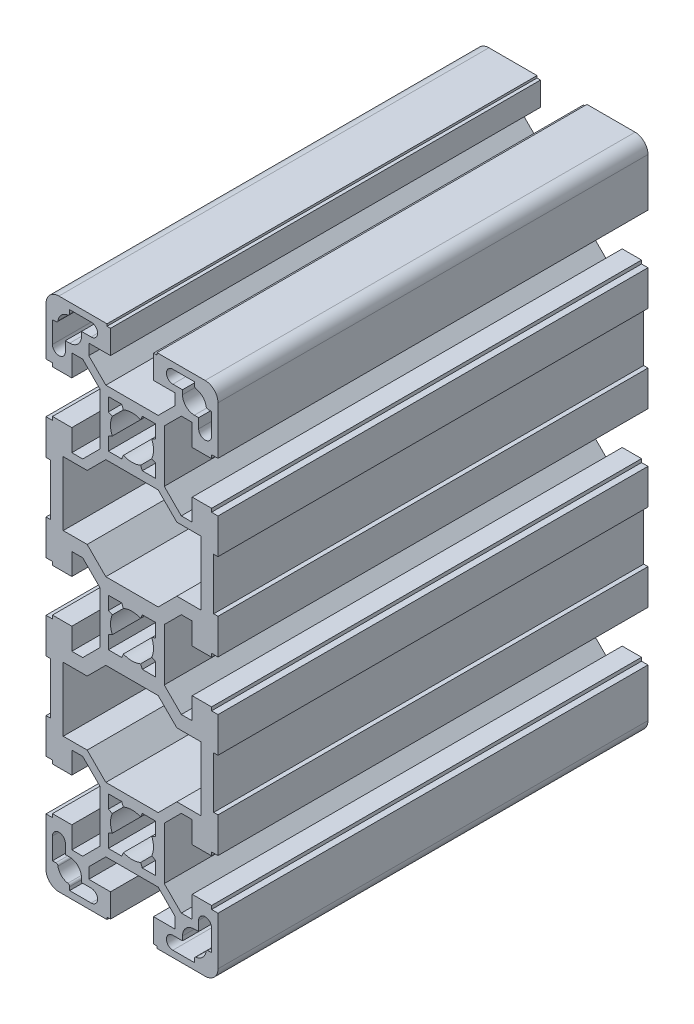
SolidWorks part; units mm, degrees
ref_plane "Front Plane" through (0, 0, 0) normal (0, 0, 1) x (1, 0, 0)
ref_plane "Top Plane" through (0, 0, 0) normal (0, 1, 0) x (1, 0, 0)
ref_plane "Right Plane" through (0, 0, 0) normal (1, 0, 0) x (0, 0, -1)
sketch "Sketch1" plane through (0, 0, 0) normal (0, 0, 1) x (1, 0, 0)
  line L0 (0, 69.0644) -> (0, -69.0644) construction
  line L1 (-42.1374, 0) -> (42.1374, 0) construction
  line L2 (20, -57) -> (20, -45.8)
  line L3 (11.75, -55.5) -> (11.75, -54.5)
  line L4 (5, -54) -> (5, -59.5)
  line L5 (-5, -59.5) -> (-5, -54)
  line L6 (-11.75, -54.5) -> (-11.75, -55.5)
  line L7 (-20, -45.8) -> (-20, -57)
  line L8 (5.8051, -60) -> (17, -60)
  line L9 (14.5, -58.5) -> (9.5, -58.5)
  line L10 (-17, -60) -> (-5.8051, -60)
  line L11 (-11.75, -55.5) -> (-9.5, -55.5)
  line L12 (-9.5, -58.5) -> (-14.5, -58.5)
  line L13 (-14.5, -58.5) -> (-14.5, -57.7113)
  line L14 (-5.8051, -60) -> (-5.8051, -59.5)
  line L15 (-5.8051, -59.5) -> (-5, -59.5)
  line L16 (9.5, -55.5) -> (11.75, -55.5)
  line L17 (5, -59.5) -> (5.8051, -59.5)
  line L18 (5.8051, -59.5) -> (5.8051, -60)
  line L19 (14.5, -57.7113) -> (14.5, -58.5)
  line L21 (18.5, 5) -> (14, 5)
  line L22 (11.4642, -29.95) -> (14, -29.95)
  line L23 (14, -10.05) -> (11.4642, -10.05)
  line L24 (14, -50.05) -> (11.4642, -50.05)
  line L25 (18.5, 5.8) -> (18.5, 5)
  line L26 (20, 5.8) -> (18.5, 5.8)
  line L27 (15.9974, -28.1597) -> (10.4261, -28.1597)
  line L28 (10.4261, -13.2597) -> (15.9974, -13.2597)
  line L29 (11.4642, -10.05) -> (7.5, -6.0858)
  line L30 (6.0884, -8.9219) -> (10.4261, -13.2597)
  line L31 (-7.5, -6.0858) -> (-11.4642, -10.05)
  line L32 (-20, -5.8) -> (-20, -14)
  line L33 (-14, -10.05) -> (-14, -5)
  line L34 (-10.4261, -13.2597) -> (-6.0884, -8.9219)
  line L35 (7.5, -33.9142) -> (11.4642, -29.95)
  line L36 (10.4261, -28.1597) -> (6.0858, -32.5)
  line L37 (-14, -35) -> (-14, -29.95)
  line L38 (-11.4642, -29.95) -> (-7.5, -33.9142)
  line L39 (-20, -26) -> (-20, -34.2)
  line L40 (-6.0858, -32.5) -> (-10.4261, -28.1597)
  line L41 (5.5, -42.3979) -> (5.5, -45.5)
  line L42 (-5.5, -45.5) -> (-5.5, -42.3979)
  line L43 (-7.5, -33.9142) -> (-7.5, -46.0858)
  line L44 (7.5, -46.0858) -> (7.5, -33.9142)
  line L45 (-7.5, -46.0858) -> (-11.4642, -50.05)
  line L46 (-5, -54) -> (-10.05, -54)
  line L47 (-10.05, -51.4642) -> (-6.0858, -47.5)
  line L48 (-14, -50.05) -> (-14, -45)
  line L49 (-11.4642, -50.05) -> (-14, -50.05)
  line L50 (-10.05, -54) -> (-10.05, -51.4642)
  line L51 (-15.5, -49.5) -> (-15.5, -51.75)
  line L52 (-15.5, -51.75) -> (-14.5, -51.75)
  line L53 (-18.5, -54.5) -> (-18.5, -49.5)
  line L54 (-17.7113, -54.5) -> (-18.5, -54.5)
  line L55 (-18.5, -45.8) -> (-20, -45.8)
  line L56 (-14, -45) -> (-18.5, -45)
  line L57 (-18.5, -45) -> (-18.5, -45.8)
  line L58 (6.0858, -47.5) -> (10.05, -51.4642)
  line L59 (11.4642, -50.05) -> (7.5, -46.0858)
  line L60 (10.05, -51.4642) -> (10.05, -54)
  line L61 (10.05, -54) -> (5, -54)
  line L62 (2.3979, -45.5) -> (1.9983, -44.5833)
  line L63 (-6.0858, -47.5) -> (6.0858, -47.5)
  line L64 (-1.9983, -44.5833) -> (-2.3979, -45.5)
  line L65 (-2.3979, -45.5) -> (-5.5, -45.5)
  line L66 (5.5, -45.5) -> (2.3979, -45.5)
  line L67 (-20, -34.2) -> (-18.5, -34.2)
  line L68 (-18.5, -34.2) -> (-18.5, -35)
  line L69 (-18.5, -35) -> (-14, -35)
  line L70 (5.5, -34.5) -> (5.5, -37.6021)
  line L71 (-5.5, -37.6021) -> (-5.5, -34.5)
  line L72 (-5.5, -42.3979) -> (-4.5833, -41.9983)
  line L73 (-4.5833, -38.0017) -> (-5.5, -37.6021)
  line L74 (5.5, -37.6021) -> (4.5833, -38.0017)
  line L75 (4.5833, -41.9983) -> (5.5, -42.3979)
  line L76 (1.9983, -35.4167) -> (2.3979, -34.5)
  line L77 (6.0858, -32.5) -> (-6.0858, -32.5)
  line L78 (-5.5, -34.5) -> (-2.3979, -34.5)
  line L79 (-2.3979, -34.5) -> (-1.9983, -35.4167)
  line L80 (2.3979, -34.5) -> (5.5, -34.5)
  line L81 (-15.9974, -28.1597) -> (-15.9974, -13.2597)
  line L82 (-19, -14) -> (-19, -26)
  line L83 (-19, -26) -> (-20, -26)
  line L84 (-14, -29.95) -> (-11.4642, -29.95)
  line L85 (-10.4261, -28.1597) -> (-15.9974, -28.1597)
  line L86 (-20, -14) -> (-19, -14)
  line L87 (-11.4642, -10.05) -> (-14, -10.05)
  line L88 (-15.9974, -13.2597) -> (-10.4261, -13.2597)
  line L89 (19, 14) -> (20, 14)
  line L90 (20, 26) -> (19, 26)
  line L91 (15.9974, 13.2597) -> (15.9974, 28.1597)
  line L92 (19, 26) -> (19, 14)
  line L93 (7.5, -6.0858) -> (7.5, 6.0858)
  line L94 (-7.5, 6.0858) -> (-7.5, -6.0858)
  line L95 (-18.5, -5.8) -> (-20, -5.8)
  line L96 (-14, -5) -> (-18.5, -5)
  line L97 (-18.5, -5) -> (-18.5, -5.8)
  line L98 (5.5, -2.3979) -> (5.5, -5.5)
  line L99 (-5.5, -5.5) -> (-5.5, -2.3979)
  line L100 (-6.0884, -8.9219) -> (6.0884, -8.9219)
  line L101 (2.3979, -5.5) -> (1.9983, -4.5833)
  line L102 (-2.3979, -5.5) -> (-5.5, -5.5)
  line L103 (-1.9983, -4.5833) -> (-2.3979, -5.5)
  line L104 (5.5, -5.5) -> (2.3979, -5.5)
  line L105 (-5.5, -2.3979) -> (-4.5833, -1.9983)
  line L106 (14, 35) -> (18.5, 35)
  line L107 (18.5, 34.2) -> (20, 34.2)
  line L108 (4.5833, -1.9983) -> (5.5, -2.3979)
  line L109 (18.5, 35) -> (18.5, 34.2)
  line L110 (18.5, 45) -> (14, 45)
  line L111 (18.5, 45.8) -> (18.5, 45)
  line L112 (20, 45.8) -> (18.5, 45.8)
  line L113 (18.5, 54.5) -> (17.7113, 54.5)
  line L114 (18.5, 49.5) -> (18.5, 54.5)
  line L115 (15.5, 51.75) -> (15.5, 49.5)
  line L116 (14.5, 51.75) -> (15.5, 51.75)
  line L117 (14, 45) -> (14, 50.05)
  line L118 (14, 29.95) -> (14, 35)
  line L119 (20, 34.2) -> (20, 26)
  line L120 (14, 5) -> (14, 10.05)
  line L121 (20, 14) -> (20, 5.8)
  line L122 (4.5833, 1.9983) -> (5.5, 2.3979)
  line L123 (-5.5, 2.3979) -> (-4.5833, 1.9983)
  line L124 (5.5, 5.5) -> (2.3979, 5.5)
  line L125 (-1.9983, 4.5833) -> (-2.3979, 5.5)
  line L126 (-2.3979, 5.5) -> (-5.5, 5.5)
  line L127 (2.3979, 5.5) -> (1.9983, 4.5833)
  line L128 (-6.0884, 8.9219) -> (6.0884, 8.9219)
  line L129 (-5.5, 5.5) -> (-5.5, 2.3979)
  line L130 (5.5, 2.3979) -> (5.5, 5.5)
  line L131 (-18.5, 5) -> (-18.5, 5.8)
  line L132 (-14, 5) -> (-18.5, 5)
  line L133 (-18.5, 5.8) -> (-20, 5.8)
  line L134 (-15.9974, 13.2597) -> (-10.4261, 13.2597)
  line L135 (-11.4642, 10.05) -> (-14, 10.05)
  line L136 (-20, 14) -> (-19, 14)
  line L137 (-10.4261, 28.1597) -> (-15.9974, 28.1597)
  line L138 (-14, 29.95) -> (-11.4642, 29.95)
  line L139 (-19, 26) -> (-20, 26)
  line L140 (-19, 14) -> (-19, 26)
  line L141 (-15.9974, 28.1597) -> (-15.9974, 13.2597)
  line L142 (2.3979, 34.5) -> (5.5, 34.5)
  line L143 (-2.3979, 34.5) -> (-1.9983, 35.4167)
  line L144 (-5.5, 34.5) -> (-2.3979, 34.5)
  line L145 (6.0858, 32.5) -> (-6.0858, 32.5)
  line L146 (1.9983, 35.4167) -> (2.3979, 34.5)
  line L147 (20, -14) -> (20, -5.8)
  line L148 (14, -5) -> (14, -10.05)
  line L149 (20, -34.2) -> (20, -26)
  line L150 (14, -29.95) -> (14, -35)
  line L151 (14, -45) -> (14, -50.05)
  line L152 (14.5, -51.75) -> (15.5, -51.75)
  line L153 (15.5, -51.75) -> (15.5, -49.5)
  line L154 (18.5, -49.5) -> (18.5, -54.5)
  line L155 (18.5, -54.5) -> (17.7113, -54.5)
  line L156 (20, -45.8) -> (18.5, -45.8)
  line L157 (18.5, -45.8) -> (18.5, -45)
  line L158 (18.5, -45) -> (14, -45)
  line L159 (18.5, -35) -> (18.5, -34.2)
  line L160 (18.5, -34.2) -> (20, -34.2)
  line L161 (14, -35) -> (18.5, -35)
  line L162 (19, -26) -> (19, -14)
  line L163 (15.9974, -13.2597) -> (15.9974, -28.1597)
  line L164 (20, -26) -> (19, -26)
  line L165 (19, -14) -> (20, -14)
  line L166 (4.5833, 41.9983) -> (5.5, 42.3979)
  line L167 (5.5, 37.6021) -> (4.5833, 38.0017)
  line L168 (20, -5.8) -> (18.5, -5.8)
  line L169 (18.5, -5.8) -> (18.5, -5)
  line L170 (18.5, -5) -> (14, -5)
  line L171 (-4.5833, 38.0017) -> (-5.5, 37.6021)
  line L172 (-5.5, 42.3979) -> (-4.5833, 41.9983)
  line L173 (-5.5, 37.6021) -> (-5.5, 34.5)
  line L174 (5.5, 34.5) -> (5.5, 37.6021)
  line L175 (-18.5, 35) -> (-14, 35)
  line L176 (-18.5, 34.2) -> (-18.5, 35)
  line L177 (-20, 34.2) -> (-18.5, 34.2)
  line L178 (5.5, 45.5) -> (2.3979, 45.5)
  line L179 (-2.3979, 45.5) -> (-5.5, 45.5)
  line L180 (-1.9983, 44.5833) -> (-2.3979, 45.5)
  line L181 (-6.0858, 47.5) -> (6.0858, 47.5)
  line L182 (2.3979, 45.5) -> (1.9983, 44.5833)
  line L183 (10.05, 54) -> (5, 54)
  line L184 (10.05, 51.4642) -> (10.05, 54)
  line L185 (11.4642, 50.05) -> (7.5, 46.0858)
  line L186 (6.0858, 47.5) -> (10.05, 51.4642)
  line L187 (-18.5, 45) -> (-18.5, 45.8)
  line L188 (-14, 45) -> (-18.5, 45)
  line L189 (-18.5, 45.8) -> (-20, 45.8)
  line L190 (-17.7113, 54.5) -> (-18.5, 54.5)
  line L191 (-18.5, 54.5) -> (-18.5, 49.5)
  line L192 (-15.5, 51.75) -> (-14.5, 51.75)
  line L193 (-15.5, 49.5) -> (-15.5, 51.75)
  line L194 (-10.05, 54) -> (-10.05, 51.4642)
  line L195 (-11.4642, 50.05) -> (-14, 50.05)
  line L196 (-14, 50.05) -> (-14, 45)
  line L197 (-10.05, 51.4642) -> (-6.0858, 47.5)
  line L198 (-5, 54) -> (-10.05, 54)
  line L199 (-7.5, 46.0858) -> (-11.4642, 50.05)
  line L200 (7.5, 46.0858) -> (7.5, 33.9142)
  line L201 (-7.5, 33.9142) -> (-7.5, 46.0858)
  line L202 (-5.5, 45.5) -> (-5.5, 42.3979)
  line L203 (5.5, 42.3979) -> (5.5, 45.5)
  line L204 (-6.0858, 32.5) -> (-10.4261, 28.1597)
  line L205 (-20, 26) -> (-20, 34.2)
  line L206 (-11.4642, 29.95) -> (-7.5, 33.9142)
  line L207 (-14, 35) -> (-14, 29.95)
  line L208 (10.4261, 28.1597) -> (6.0858, 32.5)
  line L209 (7.5, 33.9142) -> (11.4642, 29.95)
  line L210 (-10.4261, 13.2597) -> (-6.0884, 8.9219)
  line L211 (-14, 10.05) -> (-14, 5)
  line L212 (-20, 5.8) -> (-20, 14)
  line L213 (-7.5, 6.0858) -> (-11.4642, 10.05)
  line L214 (6.0884, 8.9219) -> (10.4261, 13.2597)
  line L215 (11.4642, 10.05) -> (7.5, 6.0858)
  line L216 (10.4261, 13.2597) -> (15.9974, 13.2597)
  line L217 (15.9974, 28.1597) -> (10.4261, 28.1597)
  line L218 (14, 50.05) -> (11.4642, 50.05)
  line L219 (14, 10.05) -> (11.4642, 10.05)
  line L220 (11.4642, 29.95) -> (14, 29.95)
  line L221 (14.5, 57.7113) -> (14.5, 58.5)
  line L222 (5.8051, 59.5) -> (5.8051, 60)
  line L223 (5, 59.5) -> (5.8051, 59.5)
  line L224 (9.5, 55.5) -> (11.75, 55.5)
  line L225 (-5.8051, 59.5) -> (-5, 59.5)
  line L226 (-5.8051, 60) -> (-5.8051, 59.5)
  line L227 (-14.5, 58.5) -> (-14.5, 57.7113)
  line L228 (-9.5, 58.5) -> (-14.5, 58.5)
  line L229 (-11.75, 55.5) -> (-9.5, 55.5)
  line L230 (-17, 60) -> (-5.8051, 60)
  line L231 (14.5, 58.5) -> (9.5, 58.5)
  line L232 (5.8051, 60) -> (17, 60)
  line L233 (-20, 45.8) -> (-20, 57)
  line L234 (-11.75, 54.5) -> (-11.75, 55.5)
  line L235 (-5, 59.5) -> (-5, 54)
  line L236 (5, 54) -> (5, 59.5)
  line L237 (11.75, 55.5) -> (11.75, 54.5)
  line L238 (20, 57) -> (20, 45.8)
  arc A0 (18.5, 49.5) -> (15.5, 49.5) centre (17, 49.5) cw
  arc A1 (-1.9983, 4.5833) -> (1.9983, 4.5833) centre (0, 0) cw
  arc A2 (17.7113, -54.5) -> (17.2173, -54.9231) centre (17.7113, -55) ccw
  arc A3 (-17.2173, -54.9231) -> (-17.7113, -54.5) centre (-17.7113, -55) ccw
  arc A4 (-9.5, -58.5) -> (-9.5, -55.5) centre (-9.5, -57) ccw
  arc A5 (-20, -57) -> (-17, -60) centre (-17, -57) ccw
  arc A6 (-14.5, -57.7113) -> (-14.9231, -57.2173) centre (-15, -57.7113) ccw
  arc A7 (-17.2173, -54.9231) -> (-14.9231, -57.2173) centre (-14.5, -54.5) ccw
  arc A8 (9.5, -55.5) -> (9.5, -58.5) centre (9.5, -57) ccw
  arc A9 (14.9231, -57.2173) -> (17.2173, -54.9231) centre (14.5, -54.5) ccw
  arc A10 (14.9231, -57.2173) -> (14.5, -57.7113) centre (15, -57.7113) ccw
  arc A11 (17, -60) -> (20, -57) centre (17, -57) ccw
  arc A12 (14.5, -51.75) -> (11.75, -54.5) centre (14.5, -54.5) ccw
  arc A13 (-15.5, -49.5) -> (-18.5, -49.5) centre (-17, -49.5) ccw
  arc A14 (-11.75, -54.5) -> (-14.5, -51.75) centre (-14.5, -54.5) ccw
  arc A15 (-1.9983, -44.5833) -> (1.9983, -44.5833) centre (0, -40) ccw
  arc A16 (-4.5833, -38.0017) -> (-4.5833, -41.9983) centre (0, -40) ccw
  arc A17 (4.5833, -41.9983) -> (4.5833, -38.0017) centre (0, -40) ccw
  arc A18 (1.9983, -35.4167) -> (-1.9983, -35.4167) centre (0, -40) ccw
  arc A19 (-1.9983, -4.5833) -> (1.9983, -4.5833) centre (0, 0) ccw
  arc A20 (-4.5833, 1.9983) -> (-4.5833, -1.9983) centre (0, 0) ccw
  arc A21 (4.5833, -1.9983) -> (4.5833, 1.9983) centre (0, 0) ccw
  arc A22 (1.9983, 35.4167) -> (-1.9983, 35.4167) centre (0, 40) cw
  arc A23 (4.5833, 41.9983) -> (4.5833, 38.0017) centre (0, 40) cw
  arc A24 (18.5, -49.5) -> (15.5, -49.5) centre (17, -49.5) ccw
  arc A25 (-4.5833, 38.0017) -> (-4.5833, 41.9983) centre (0, 40) cw
  arc A26 (-1.9983, 44.5833) -> (1.9983, 44.5833) centre (0, 40) cw
  arc A27 (-11.75, 54.5) -> (-14.5, 51.75) centre (-14.5, 54.5) cw
  arc A28 (-15.5, 49.5) -> (-18.5, 49.5) centre (-17, 49.5) cw
  arc A29 (14.5, 51.75) -> (11.75, 54.5) centre (14.5, 54.5) cw
  arc A30 (17, 60) -> (20, 57) centre (17, 57) cw
  arc A31 (14.9231, 57.2173) -> (14.5, 57.7113) centre (15, 57.7113) cw
  arc A32 (14.9231, 57.2173) -> (17.2173, 54.9231) centre (14.5, 54.5) cw
  arc A33 (9.5, 55.5) -> (9.5, 58.5) centre (9.5, 57) cw
  arc A34 (-17.2173, 54.9231) -> (-14.9231, 57.2173) centre (-14.5, 54.5) cw
  arc A35 (-14.5, 57.7113) -> (-14.9231, 57.2173) centre (-15, 57.7113) cw
  arc A36 (-20, 57) -> (-17, 60) centre (-17, 57) cw
  arc A37 (-9.5, 58.5) -> (-9.5, 55.5) centre (-9.5, 57) cw
  arc A38 (-17.2173, 54.9231) -> (-17.7113, 54.5) centre (-17.7113, 55) cw
  arc A39 (17.7113, 54.5) -> (17.2173, 54.9231) centre (17.7113, 55) cw
  point P247 (-7.5, 0)
  point P249 (7.5, 0)
  dimension "D3" = 10
  dimension "D1" = 120
  dimension "D2" = 40
extrude "Extrude1" add sketch "Sketch1" against normal blind 100
